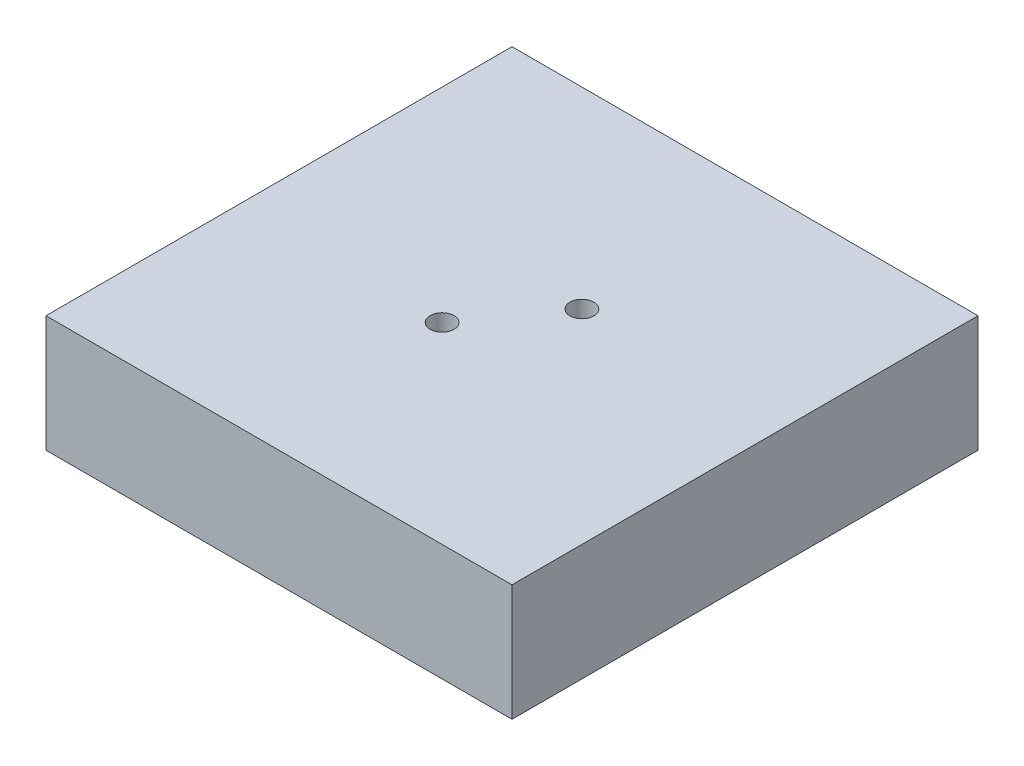
SolidWorks part; units mm, degrees
ref_plane "Front Plane" through (0, 0, 0) normal (0, 0, 1) x (1, 0, 0)
ref_plane "Top Plane" through (0, 0, 0) normal (0, 1, 0) x (1, 0, 0)
ref_plane "Right Plane" through (0, 0, 0) normal (1, 0, 0) x (0, 0, -1)
sketch "Sketch1" plane through (0, 0, 0) normal (0, 1, 0) x (1, 0, 0)
  line L1 (-20, 20) -> (20, 20)
  line L2 (-20, 20) -> (-20, -20)
  line L3 (-20, -20) -> (20, -20)
  line L4 (20, 20) -> (20, -20)
  point P4 (0, -20)
  point P6 (-20, 0)
  dimension "D1" = 40
  dimension "D2" = 40
extrude "Boss-Extrude1" add sketch "Sketch1" along normal blind 10
hole_wizard "M2.5 Tapped Hole1" positions "Sketch2" profile "Sketch3" tap size "M2.5" standard "ISO" end condition through all
sketch "Sketch2" plane through (0, 10, 0) normal (0, 1, 0) x (1, 0, 0)
  line L2 (-2.5, 3.5) -> (2.5, 3.5)
  line L3 (-2.5, 3.5) -> (-2.5, -3.5)
  line L4 (-2.5, -3.5) -> (2.5, -3.5)
  line L5 (2.5, 3.5) -> (2.5, -3.5)
  point P0 (-2.5, -3.5)
  point P2 (2.5, 3.5)
  point P310 (-3.3225, -3.9491)
  point P311 (6.7943, 7.2924)
  point P313 (0, -3.5)
  point P315 (-2.5, 0)
  dimension "D1" = 7
  dimension "D2" = 5
sketch "Sketch3" plane through (-2.5, 10, 3.5) normal (1, 0, 0) x (0, 0, 1)
  line L0 (0, 0) -> (0, 10)
  line L1 (0, 10) -> (1.025, 10)
  line L2 (1.025, 10) -> (1.025, 0)
  line L5 (1.025, 0) -> (0, 0)
  line L11 (0, -6.35) -> (0, 107.95) construction
  dimension "Thru Tap Drill Dia." = 2.05
  dimension "Thru Tap Drill Depth" = 10
cosmetic thread "Hole Thread1"
cosmetic thread "Hole Thread2"
